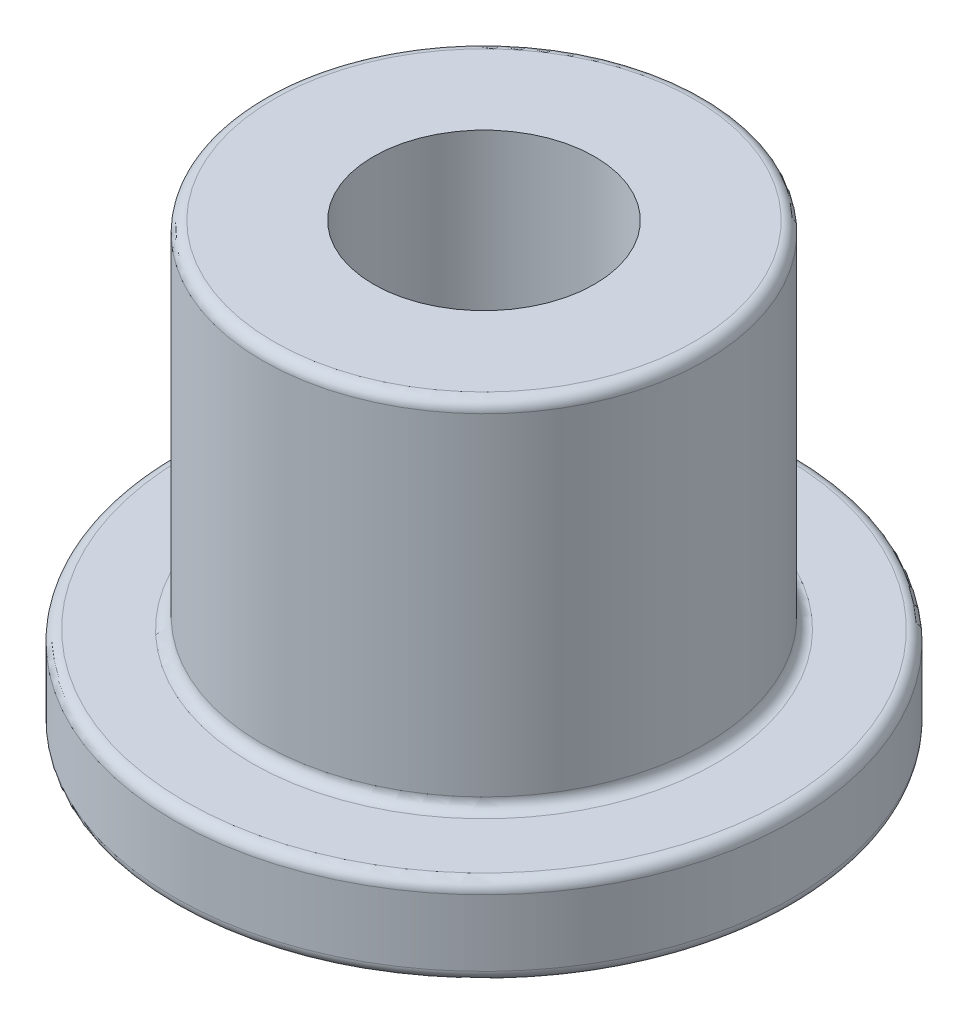
SolidWorks part; units mm, degrees
material "AISI 304"
ref_plane "Alzado" through (0, 0, 0) normal (0, 0, 1) x (1, 0, 0)
ref_plane "Planta" through (0, 0, 0) normal (0, 1, 0) x (1, 0, 0)
ref_plane "Vista lateral" through (0, 0, 0) normal (1, 0, 0) x (0, 0, -1)
sketch "Croquis1" plane through (0, 0, 0) normal (0, 1, 0) x (1, 0, 0)
  circle A0 centre (0, 0) radius 7
  dimension "D1" = 14
extrude "Saliente-Extruir1" add sketch "Croquis1" along normal blind 2
sketch "Croquis2" plane through (0, 2, 0) normal (0, 1, 0) x (1, 0, 0)
  circle A0 centre (0, 0) radius 5
  dimension "D1" = 10
extrude "Saliente-Extruir2" add sketch "Croquis2" along normal blind 8
sketch "Croquis3" plane through (0, 10, 0) normal (0, 1, 0) x (1, 0, 0)
  circle A0 centre (0, 0) radius 2.5
  dimension "D1" = 5
extrude "Cortar-Extruir1" cut sketch "Croquis3" against normal blind 18
fillet "Redondeo1" radius 0.25 4 edges at (0, 10, 5) (0, 2, 5) (0, 2, 7) (0, 0, 7)
